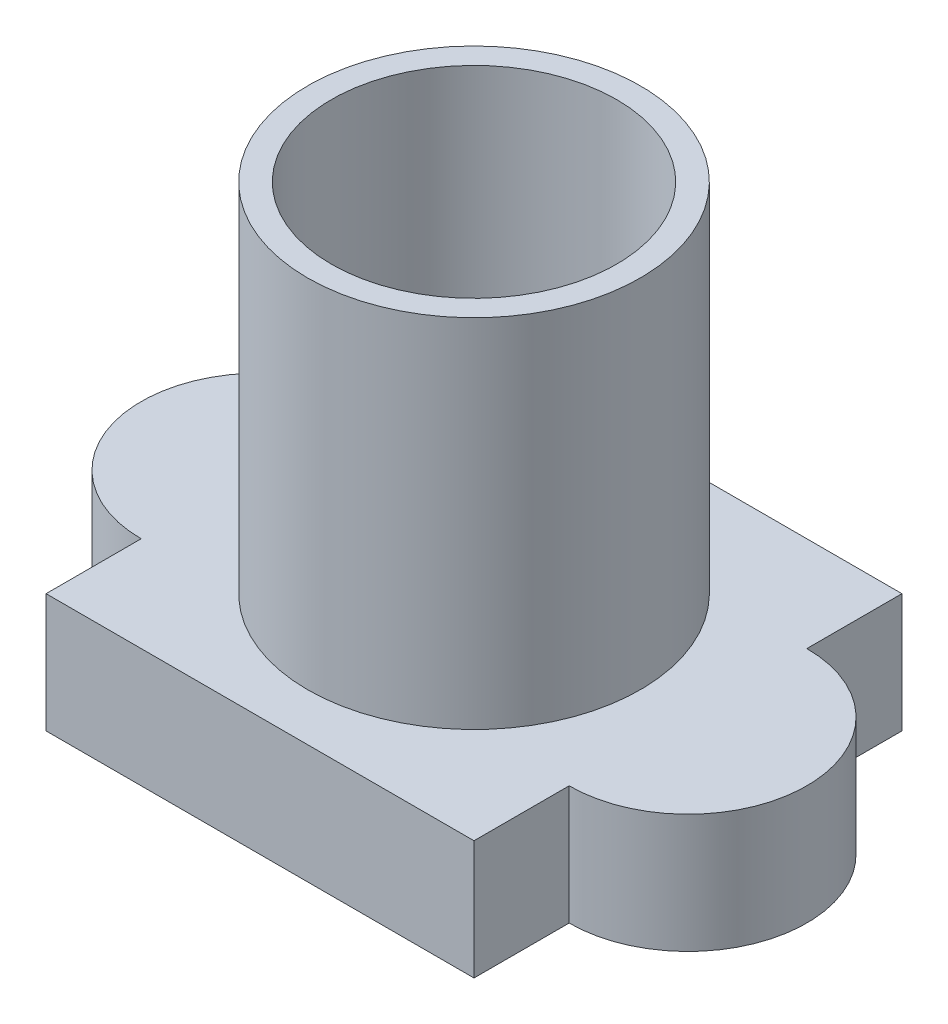
SolidWorks part; units mm, degrees
ref_plane "Front Plane" through (0, 0, 0) normal (0, 0, 1) x (1, 0, 0)
ref_plane "Top Plane" through (0, 0, 0) normal (0, 1, 0) x (1, 0, 0)
ref_plane "Right Plane" through (0, 0, 0) normal (1, 0, 0) x (0, 0, -1)
sketch "Sketch1" plane through (0, 0, 0) normal (0, 1, 0) x (1, 0, 0)
  line L0 (-9, 0) -> (9, 0) construction
  line L1 (-9, 5) -> (9, 5)
  line L2 (-9, -5) -> (9, -5)
  line L3 (0, 0) -> (0, 23.9692) construction
  line L4 (-9, 5) -> (-9, 9)
  line L5 (-9, 9) -> (9, 9)
  line L6 (9, 9) -> (9, 5)
  line L7 (9, -5) -> (9, -9)
  line L8 (9, -9) -> (-9, -9)
  line L9 (-9, -9) -> (-9, -5)
  arc A0 (-9, 5) -> (-9, -5) centre (-9, 0) ccw
  arc A1 (9, -5) -> (9, 5) centre (9, 0) ccw
  point P2 (0, 0)
  dimension "D1" = 5
  dimension "D2" = 18
  dimension "D3" = 18
extrude "Boss-Extrude1" add sketch "Sketch1" along normal blind 5 contours L6 L5 L4 L1 | L9 L8 L7 L2 | L2 A1 L1 A0
sketch "Sketch2" plane through (0, 5, 0) normal (0, 1, 0) x (1, 0, 0)
  circle A0 centre (0, 0) radius 7
  dimension "D1" = 14
extrude "Boss-Extrude2" add sketch "Sketch2" along normal blind 15
sketch "Sketch3" plane through (0, 20, 0) normal (0, 1, 0) x (1, 0, 0)
  circle A0 centre (0, 0) radius 6
  dimension "D1" = 12
extrude "Cut-Extrude1" cut sketch "Sketch3" against normal through all
sketch "Sketch4" plane through (0, 0, 0) normal (0, -1, 0) x (1, 0, 0)
  line L12 (8, -8) -> (8, -3.873)
  line L13 (8, 3.873) -> (8, 8)
  line L14 (8, 8) -> (-8, 8)
  line L15 (-8, 8) -> (-8, 3.873)
  line L16 (-8, -3.873) -> (-8, -8)
  line L17 (-8, -8) -> (8, -8)
  line L18 (8, -8) -> (8, -3.873)
  line L19 (8, 3.873) -> (8, 8)
  line L20 (8, 8) -> (-8, 8)
  line L21 (-8, 8) -> (-8, 3.873)
  line L22 (-8, -3.873) -> (-8, -8)
  line L23 (-8, -8) -> (8, -8)
  arc A4 (8, -3.873) -> (8, 3.873) centre (9, 0) ccw
  arc A5 (-8, 3.873) -> (-8, -3.873) centre (-9, 0) ccw
  arc A6 (8, -3.873) -> (8, 3.873) centre (9, 0) ccw
  arc A7 (-8, 3.873) -> (-8, -3.873) centre (-9, 0) ccw
  dimension "D1" = 1
extrude "Cut-Extrude2" cut sketch "Sketch4" against normal blind 4
